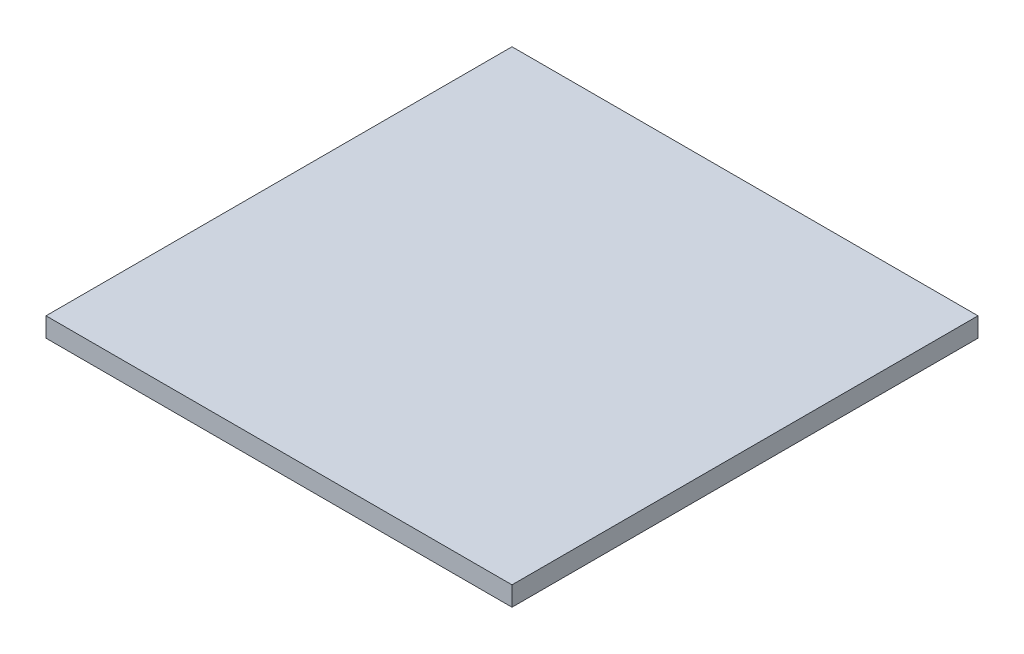
SolidWorks part; units mm, degrees
material "A-Glass Fiber"
ref_plane "Front" through (0, 0, 0) normal (0, 0, 1) x (1, 0, 0)
ref_plane "Top" through (0, 0, 0) normal (0, 1, 0) x (1, 0, 0)
ref_plane "Right" through (0, 0, 0) normal (1, 0, 0) x (0, 0, -1)
sketch "Sketch1" plane through (0, 0, 0) normal (0, 1, 0) x (1, 0, 0)
  line L1 (-18, -18) -> (18, -18)
  line L2 (-18, -18) -> (-18, 18)
  line L3 (-18, 18) -> (18, 18)
  line L4 (18, -18) -> (18, 18)
  line L5 (-18, -18) -> (18, 18) construction
  line L6 (-18, 18) -> (18, -18) construction
  point P0 (0, 0)
  dimension "D1" = 36
  dimension "D2" = 36
extrude "Boss-Extrude1" add sketch "Sketch1" along normal blind 1.5
